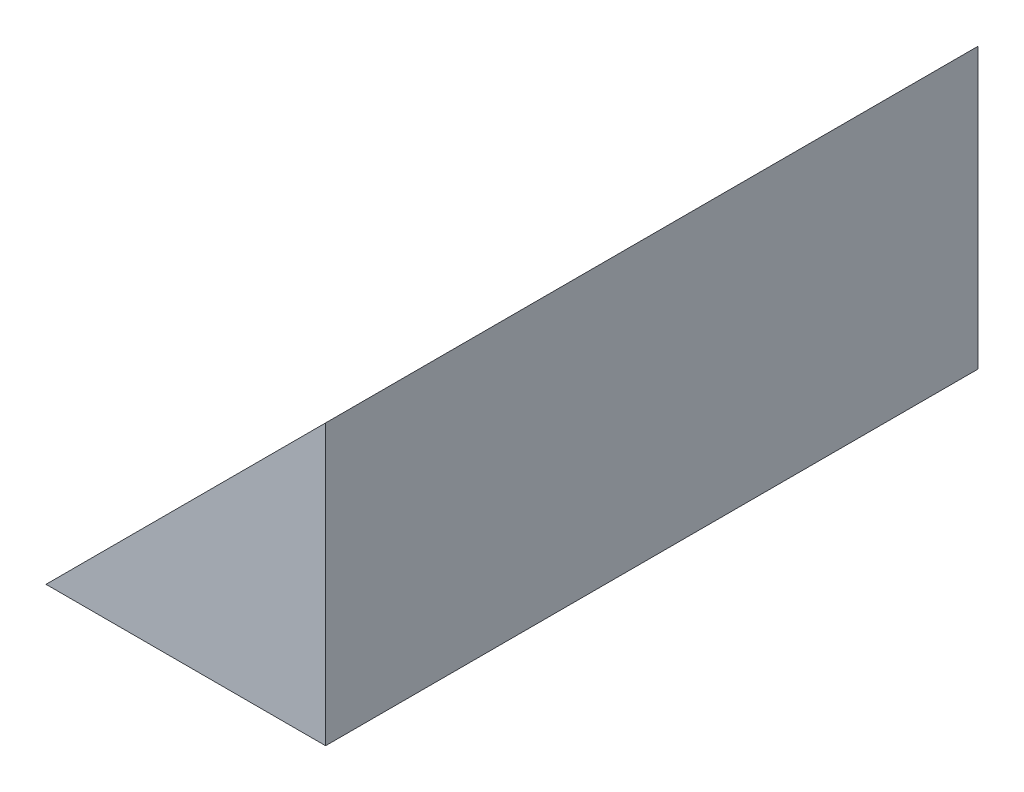
SolidWorks part; units mm, degrees
material "Pine"
ref_plane "Front Plane" through (0, 0, 0) normal (0, 0, 1) x (1, 0, 0)
ref_plane "Top Plane" through (0, 0, 0) normal (0, 1, 0) x (1, 0, 0)
ref_plane "Right Plane" through (0, 0, 0) normal (1, 0, 0) x (0, 0, -1)
sketch "Sketch1" plane through (0, 0, 0) normal (0, 1, 0) x (1, 0, 0)
  line L1 (0, 0) -> (38.1, 0)
  line L2 (0, 0) -> (0, 88.9)
  line L3 (0, 88.9) -> (38.1, 88.9)
  line L4 (38.1, 0) -> (38.1, 88.9)
  dimension "D1" = 88.9
  dimension "D2" = 38.1
extrude "Boss-Extrude1" add sketch "Sketch1" along normal blind 38.1
sketch "Sketch2" plane through (0, 0, 0) normal (0, 0, 1) x (1, 0, 0)
  line L0 (0, 0) -> (38.1, 38.1)
  line L1 (0, 38.1) -> (38.1, 38.1) construction
  line L2 (38.1, 38.1) -> (0, 38.1)
  line L3 (0, 38.1) -> (0, 0)
  dimension "D1" = 38.1
  dimension "D2" = 38.1
extrude "Cut-Extrude1" cut sketch "Sketch2" against normal through all
